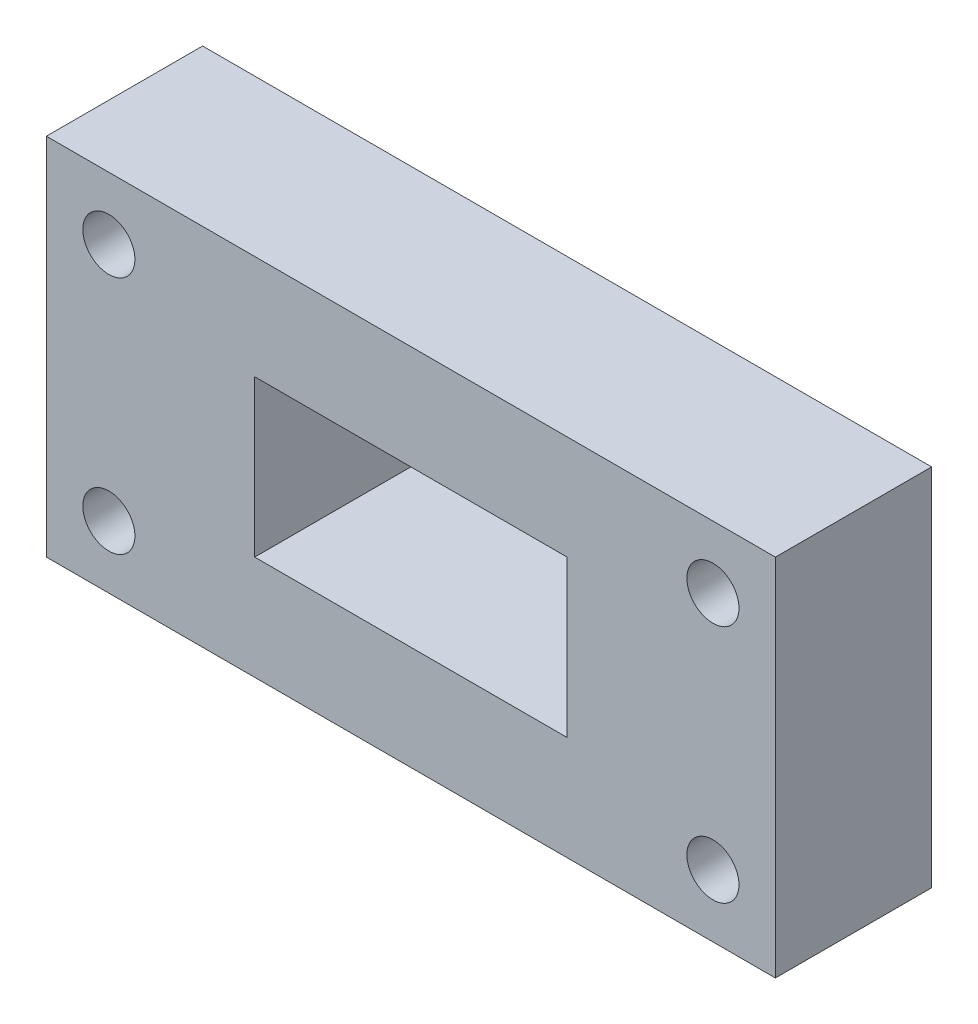
SolidWorks part; units mm, degrees
material "AISI 1020"
ref_plane "Plano frontal" through (0, 0, 0) normal (0, 0, 1) x (1, 0, 0)
ref_plane "Plano superior" through (0, 0, 0) normal (0, 1, 0) x (1, 0, 0)
ref_plane "Plano direito" through (0, 0, 0) normal (1, 0, 0) x (0, 0, -1)
sketch "Esboço1" plane through (0, 0, 0) normal (0, 0, 1) x (1, 0, 0)
  line L1 (70, 35) -> (-70, 35)
  line L2 (70, 35) -> (70, -35)
  line L3 (70, -35) -> (-70, -35)
  line L4 (-70, 35) -> (-70, -35)
  line L5 (70, 35) -> (-70, -35) construction
  line L6 (70, -35) -> (-70, 35) construction
  point P0 (0, 0)
  dimension "D1" = 140
  dimension "D2" = 70
extrude "Ressalto-extrusão1" add sketch "Esboço1" along normal blind 30
sketch "Esboço2" plane through (0, 0, 30) normal (0, 0, 1) x (1, 0, 0)
  line L1 (30, 15) -> (-30, 15)
  line L2 (30, 15) -> (30, -15)
  line L3 (30, -15) -> (-30, -15)
  line L4 (-30, 15) -> (-30, -15)
  line L5 (30, 15) -> (-30, -15) construction
  line L6 (30, -15) -> (-30, 15) construction
  point P0 (0, 0)
  dimension "D1" = 30
  dimension "D2" = 60
extrude "Corte-extrusão1" cut sketch "Esboço2" against normal through all
sketch "Esboço3" plane through (0, 0, 30) normal (0, 0, 1) x (1, 0, 0)
  line L1 (58, 23) -> (-58, 23) construction
  line L2 (58, 23) -> (58, -23) construction
  line L3 (58, -23) -> (-58, -23) construction
  line L4 (-58, 23) -> (-58, -23) construction
  line L5 (58, 23) -> (-58, -23) construction
  line L6 (58, -23) -> (-58, 23) construction
  circle A0 centre (-58, 23) radius 5
  circle A1 centre (58, 23) radius 5
  circle A2 centre (58, -23) radius 5
  circle A3 centre (-58, -23) radius 5
  point P0 (0, 0)
  dimension "D3" = 10
  dimension "D1" = 116
  dimension "D2" = 46
extrude "Corte-extrusão3" cut sketch "Esboço3" against normal through all
